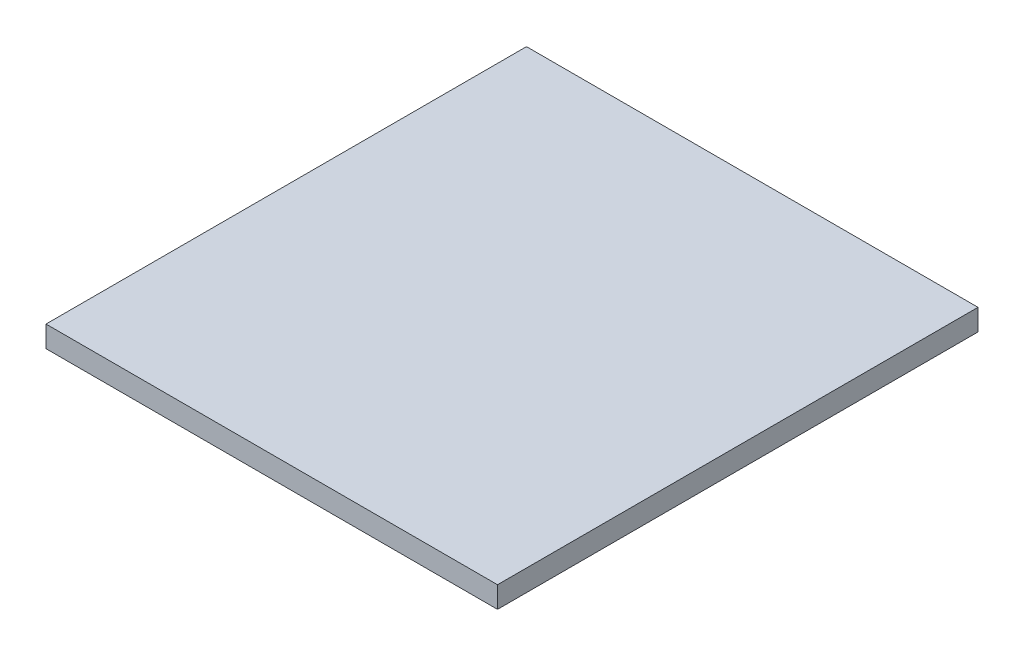
SolidWorks part; units mm, degrees
ref_plane "Front Plane" through (0, 0, 0) normal (0, 0, 1) x (1, 0, 0)
ref_plane "Top Plane" through (0, 0, 0) normal (0, 1, 0) x (1, 0, 0)
ref_plane "Right Plane" through (0, 0, 0) normal (1, 0, 0) x (0, 0, -1)
sketch "Sketch1" plane through (0, 0, 0) normal (0, 1, 0) x (1, 0, 0)
  line L5 (-211.43, -225) -> (211.43, -225)
  line L6 (-211.43, -225) -> (-211.43, 225)
  line L7 (-211.43, 225) -> (211.43, 225)
  line L8 (211.43, -225) -> (211.43, 225)
  line L9 (-211.43, -225) -> (211.43, 225) construction
  line L10 (-211.43, 225) -> (211.43, -225) construction
  point P0 (0, 0)
  dimension "D1" = 422.86
  dimension "D2" = 450
extrude "Boss-Extrude1" add sketch "Sketch1" along normal blind 20
